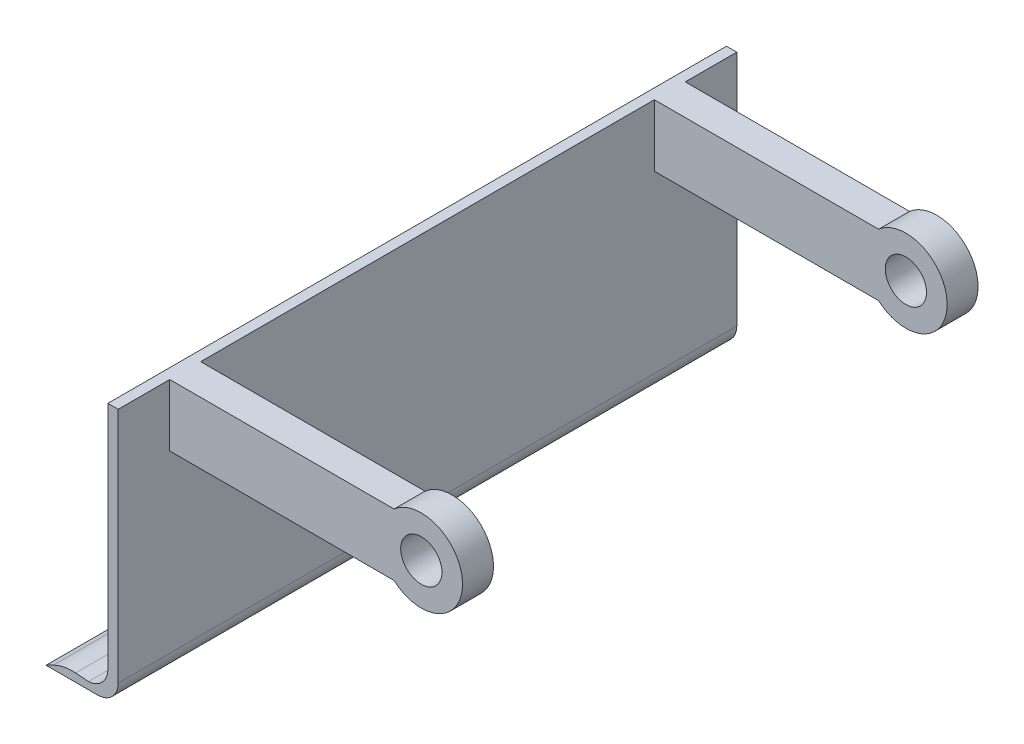
SolidWorks part; units mm, degrees
ref_plane "Plan de face" through (0, 0, 0) normal (0, 0, 1) x (1, 0, 0)
ref_plane "Plan de dessus" through (0, 0, 0) normal (0, 1, 0) x (1, 0, 0)
ref_plane "Plan de droite" through (0, 0, 0) normal (1, 0, 0) x (0, 0, -1)
sketch "Esquisse1" plane through (0, 0, 0) normal (0, 0, 1) x (1, 0, 0)
  line L0 (-5, 35) -> (-5, 13.418)
  line L1 (-14.387, 3.4368) -> (-20.6199, 3.9625)
  line L2 (0, 30) -> (0, 125)
  line L3 (0, 125) -> (-5, 125)
  line L4 (-5, 35) -> (-5, 125)
  line L5 (-31.4173, 1.8348) -> (-35, 0)
  line L6 (-35, 0) -> (-10, 0)
  line L7 (0, 10) -> (0, 30)
  arc A0 (-31.4173, 1.8348) -> (-20.6199, 3.9625) centre (-22.3009, -15.9667) cw
  arc A1 (-10, 0) -> (0, 10) centre (-10, 10) ccw
  arc A2 (-5, 13.418) -> (-14.387, 3.4368) centre (-15, 13.418) cw
  point P13 (0, 0)
  dimension "D2" = 5
  dimension "D1" = 10
  dimension "D3" = 20
  dimension "D4" = 10
  dimension "D5" = 125
  dimension "D6" = 35
extrude "Boss.-Extru.1" add sketch "Esquisse1" along normal blind 300
sketch "Esquisse3" plane through (0, 0, 0) normal (1, 0, 0) x (0, 0, -1)
  line L1 (-300, 125) -> (0, 125) construction
  line L2 (-300, 10) -> (-300, 125) construction
  line L3 (-260, 125) -> (-275, 125)
  line L4 (-260, 125) -> (-260, 95)
  line L5 (-260, 95) -> (-275, 95)
  line L6 (-275, 125) -> (-275, 95)
  line L7 (-40, 125) -> (-25, 125)
  line L8 (-40, 125) -> (-40, 95)
  line L12 (-40, 95) -> (-25, 95)
  line L13 (-25, 125) -> (-25, 95)
  dimension "D1" = 220
  dimension "D2" = 15
  dimension "D3" = 30
  dimension "D4" = 30
  dimension "D5" = 15
  dimension "D6" = 25
extrude "Boss.-Extru.2" add sketch "Esquisse3" along normal blind 115
sketch "Esquisse4" plane through (0, 0, 275) normal (0, 0, 1) x (1, 0, 0)
  line L0 (115, 125) -> (115, 95) construction
  line L1 (115, 110) -> (160.4893, 110) construction
  circle A0 centre (122, 110) radius 20
  dimension "D1" = 7
  dimension "D2" = 40
extrude "Boss.-Extru.3" add sketch "Esquisse4" against normal up to surface (15 mm away) up to face at (57.5, 110, 260)
sketch "Esquisse5" plane through (0, 0, 275) normal (0, 0, 1) x (1, 0, 0)
  circle A0 centre (122, 110) radius 10
  dimension "D1" = 20
sketch "Esquisse6" plane through (0, 0, 40) normal (0, 0, 1) x (1, 0, 0)
  circle A0 centre (122, 110) radius 20
extrude "Boss.-Extru.4" add sketch "Esquisse6" against normal up to surface (15 mm away) up to face at (57.5, 110, 25)
extrude "Enlèv. mat.-Extru.1" cut sketch "Esquisse5" against normal through all contours A0
